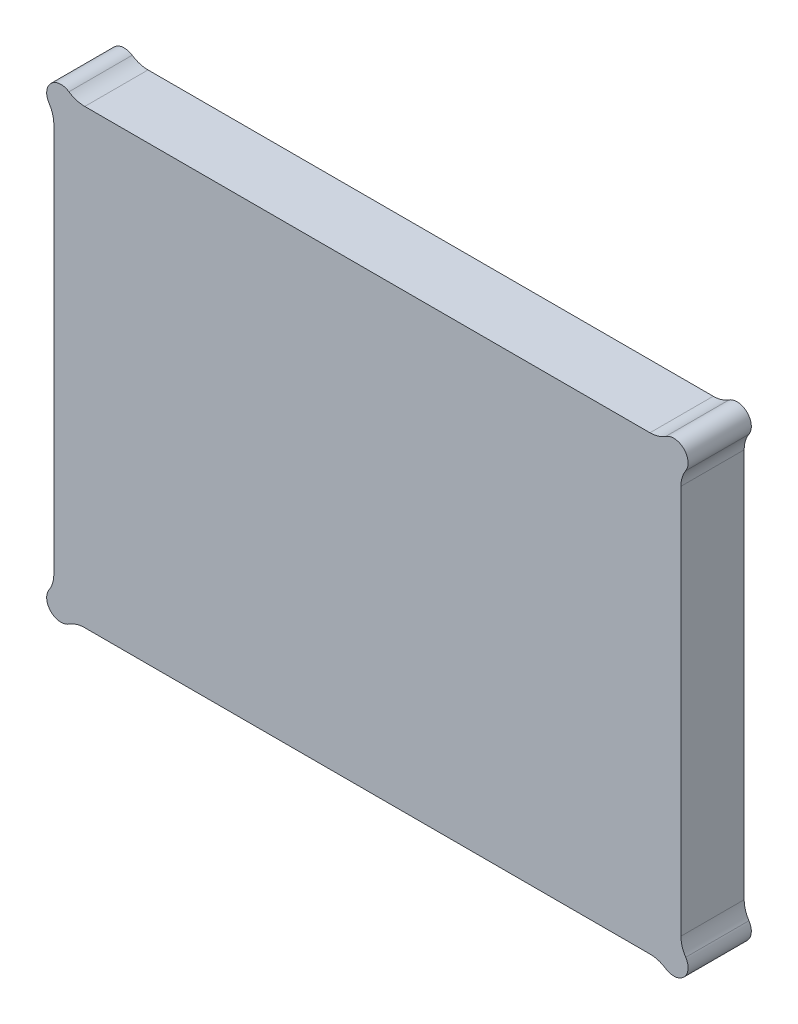
SolidWorks part; units mm, degrees
ref_plane "Front Plane" through (0, 0, 0) normal (0, 0, 1) x (1, 0, 0)
ref_plane "Top Plane" through (0, 0, 0) normal (0, 1, 0) x (1, 0, 0)
ref_plane "Right Plane" through (0, 0, 0) normal (1, 0, 0) x (0, 0, -1)
sketch "Sketch1" plane through (0, 0, 0) normal (0, 0, 1) x (1, 0, 0)
  line L1 (-148, -7) -> (7, -7) construction
  line L2 (7, -7) -> (7, 99) construction
  line L3 (7, 99) -> (-148, 99) construction
  line L4 (-148, 99) -> (-148, -7) construction
  line L5 (-148, -7) -> (7, -7) construction
  line L6 (7, -7) -> (7, 99) construction
  line L7 (7, 99) -> (-148, 99) construction
  line L8 (-148, 99) -> (-148, -7) construction
  line L9 (-158, -17) -> (17, -17)
  line L10 (17, -17) -> (17, 109)
  line L11 (17, 109) -> (-158, 109)
  line L12 (-158, 109) -> (-158, -17)
  dimension "D1" = 10
extrude "Boss-Extrude1" add sketch "Sketch1" along normal blind 2 from offset 2
sketch "Sketch2" plane through (0, 0, 2) normal (0, 0, -1) x (-1, 0, 0)
  circle A0 centre (0, 0) radius 5
  circle A1 centre (69.5, 63.5) radius 5
  circle A2 centre (0, 92) radius 5
  circle A3 centre (141, 92) radius 5
  circle A4 centre (141, 0) radius 5
  dimension "D1" = 10
extrude "Boss-Extrude2" add sketch "Sketch2" along normal up to surface (2 mm away)
fillet "Fillet1" radius 2 4 edges at (-158, -17, 3) (-158, 109, 3) (17, 109, 3) (17, -17, 3)
sketch "Sketch3" plane through (0, 0, 2) normal (0, 0, -1) x (-1, 0, 0)
  line L0 (-15, 109) -> (156, 109)
  line L1 (-15, 109) -> (156, 109)
  line L2 (-17, -15) -> (-17, 107)
  line L3 (-17, -15) -> (-17, 107)
  line L4 (156, -17) -> (-15, -17)
  line L5 (156, -17) -> (-15, -17)
  line L6 (158, 107) -> (158, -15)
  line L7 (158, 107) -> (158, -15)
  line L8 (-3, 102) -> (144, 102)
  line L9 (151, 95) -> (151, -3)
  line L10 (144, -10) -> (-3, -10)
  line L11 (-10, -3) -> (-10, 95)
  line L12 (151, 102) -> (151, -10) construction
  line L13 (-10, 102) -> (151, 102) construction
  line L14 (151, -10) -> (-10, -10) construction
  line L15 (-10, -10) -> (-10, 102) construction
  arc A0 (-15, 109) -> (-17, 107) centre (-15, 107) ccw
  arc A1 (-15, 109) -> (-17, 107) centre (-15, 107) ccw
  arc A2 (-17, -15) -> (-15, -17) centre (-15, -15) ccw
  arc A3 (-17, -15) -> (-15, -17) centre (-15, -15) ccw
  arc A4 (156, -17) -> (158, -15) centre (156, -15) ccw
  arc A5 (156, -17) -> (158, -15) centre (156, -15) ccw
  arc A6 (158, 107) -> (156, 109) centre (156, 107) ccw
  arc A7 (158, 107) -> (156, 109) centre (156, 107) ccw
  arc A8 (151, -3) -> (144, -10) centre (144, -3) cw
  arc A9 (-3, -10) -> (-10, -3) centre (-3, -3) cw
  arc A10 (-10, 95) -> (-3, 102) centre (-3, 95) cw
  arc A12 (151, 95) -> (144, 102) centre (144, 95) ccw
  arc A13 (151, 102) -> (151, 102) centre (151, 102) ccw construction
  arc A14 (151, -10) -> (151, -10) centre (151, -10) ccw construction
  arc A15 (-10, -10) -> (-10, -10) centre (-10, -10) ccw construction
  arc A16 (-10, 102) -> (-10, 102) centre (-10, 102) ccw construction
  dimension "D2" = 7
  dimension "D1" = 7
extrude "Boss-Extrude3" add sketch "Sketch3" along normal offset from surface (15.65 mm away) 2
sketch "Sketch5" plane through (0, 0, -13.65) normal (0, 0, -1) x (-1, 0, 0)
  line L0 (-10, -3) -> (-10, 95) construction
  line L1 (144, -10) -> (-3, -10) construction
  line L2 (-3, 102) -> (144, 102) construction
  line L3 (151, 95) -> (151, -3) construction
  line L4 (-10, -3) -> (-10, 95) construction
  line L5 (144, -10) -> (-3, -10) construction
  line L6 (-3, 102) -> (144, 102) construction
  line L7 (151, 95) -> (151, -3) construction
  line L8 (-3, 104) -> (144, 104)
  line L9 (153, 95) -> (153, -3)
  line L10 (144, -12) -> (-3, -12)
  line L11 (-12, -3) -> (-12, 95)
  arc A0 (-10, -3) -> (-3, -10) centre (-3, -3) ccw construction
  arc A1 (-3, 102) -> (-10, 95) centre (-3, 95) ccw construction
  arc A2 (144, -10) -> (151, -3) centre (144, -3) ccw construction
  arc A3 (151, 95) -> (144, 102) centre (144, 95) ccw construction
  arc A4 (-10, -3) -> (-3, -10) centre (-3, -3) ccw construction
  arc A5 (-3, 102) -> (-10, 95) centre (-3, 95) ccw construction
  arc A6 (144, -10) -> (151, -3) centre (144, -3) ccw construction
  arc A7 (151, 95) -> (144, 102) centre (144, 95) ccw construction
  arc A8 (153, 95) -> (144, 104) centre (144, 95) ccw
  arc A9 (144, -12) -> (153, -3) centre (144, -3) ccw
  arc A10 (-12, -3) -> (-3, -12) centre (-3, -3) ccw
  arc A11 (-3, 104) -> (-12, 95) centre (-3, 95) ccw
  dimension "D1" = 2
extrude "Cut-Extrude-Thin1" cut sketch "Sketch5" against normal blind 2.25 thin thin type one direction wall 3
sketch "Sketch8" plane through (0, 0, -13.65) normal (0, 0, -1) x (-1, 0, 0)
  circle A0 centre (156, 107) radius 4
  circle A2 centre (156, -15) radius 4
  circle A4 centre (-15, -15) radius 4
  circle A6 centre (-15, 107) radius 4
  dimension "D1" = 8
extrude "Boss-Extrude4" add sketch "Sketch8" against normal up to surface (17.65 mm away) up to face at (-70.5, 46, 4)
fillet "Fillet2" radius 8 8 edges at (-152.5359, -17, -4.825) (-158, -11.5359, -4.825) (-158, 103.5359, -4.825) (-152.5359, 109, -4.825) (11.5359, 109, -4.825) (17, 103.5359, -4.825) (17, -11.5359, -4.825) (11.5359, -17, -4.825)
